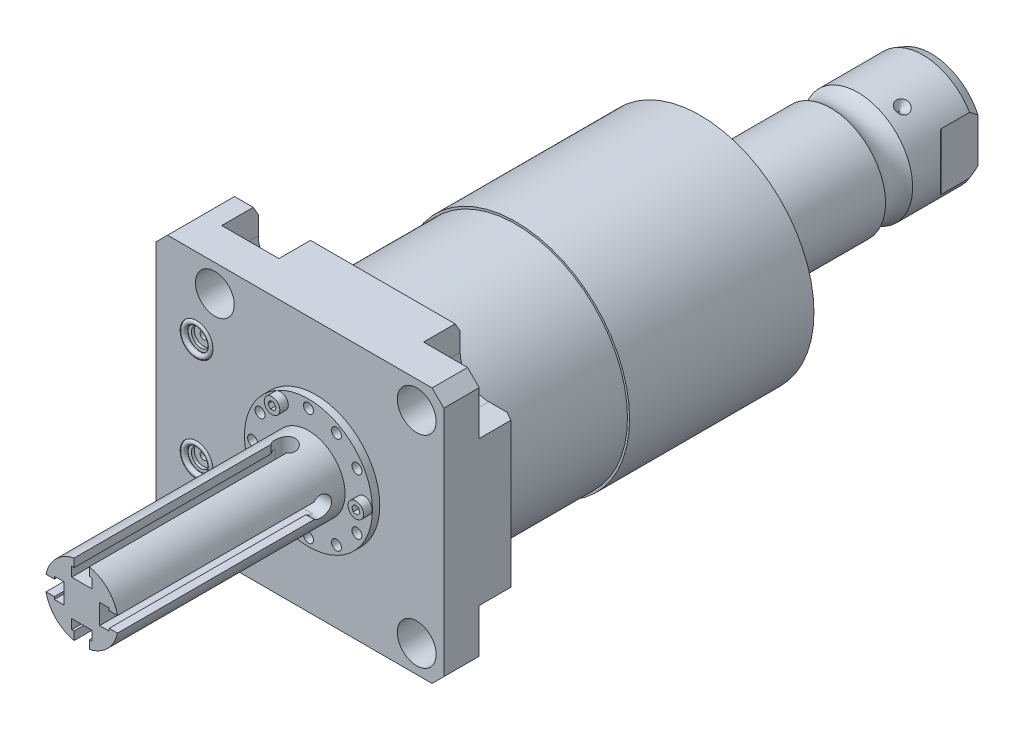
SolidWorks part; units mm, degrees
material "Alloy Steel"
ref_plane "Front Plane" through (0, 0, 0) normal (0, 0, 1) x (1, 0, 0)
ref_plane "Top Plane" through (0, 0, 0) normal (0, 1, 0) x (1, 0, 0)
ref_plane "Right Plane" through (0, 0, 0) normal (1, 0, 0) x (0, 0, -1)
sketch "Sketch1" plane through (0, 0, 0) normal (0, 0, 1) x (1, 0, 0)
  line L0 (-55.55, 44.45) -> (44.45, 44.45)
  line L1 (44.45, 44.45) -> (44.45, -44.45)
  line L2 (44.45, -44.45) -> (-55.55, -44.45)
  line L3 (-55.55, -44.45) -> (-55.55, 44.45)
  dimension "D1" = 100
  dimension "D2" = 88.9
  dimension "D3" = 44.45
  dimension "D4" = 44.45
extrude "Extrude1" add sketch "Sketch1" along normal blind 25.019
hole_wizard "Hole1" positions "Sketch22" profile "Sketch21" legacy end condition through all
sketch "Sketch22" plane through (0, 0, 0) normal (0, 0, -1) x (-1, 0, 0)
  line L0 (0, 0) -> (42.7441, 0) construction
  line L1 (0, 0.8532) -> (0, 27.5062) construction
  point P0 (-35.052, -35.052)
  point P9 (-35.052, 35.052)
  point P11 (35.052, 35.052)
  point P12 (35.052, -35.052)
  dimension "D1" = 35.052
  dimension "D2" = 35.052
sketch "Sketch21" plane through (35.052, -35.052, 0) normal (1, 0, 0) x (0, 1, 0)
  line L0 (0, 0) -> (0, 25.019)
  line L1 (0, 25.019) -> (6.7435, 25.019)
  line L2 (6.7435, 25.019) -> (6.7435, 0)
  line L3 (6.7435, 0) -> (0, 0)
  line L4 (0, 110) -> (0, -10) construction
  dimension "Diameter" = 13.487
  dimension "Depth" = 25.019
sketch "Sketch3" plane through (0, 0, 0) normal (0, 0, -1) x (-1, 0, 0)
  line L0 (-35.052, -25.1205) -> (-44.45, -25.1205)
  line L1 (-44.45, -44.45) -> (-44.45, -25.1205)
  line L2 (-44.45, 25.1205) -> (-44.45, 44.45)
  line L3 (-44.45, 25.1205) -> (-35.052, 25.1205)
  line L4 (-25.1205, 35.052) -> (-25.1205, 44.45)
  line L5 (-44.45, 44.45) -> (-25.1205, 44.45)
  line L6 (25.1205, 44.45) -> (25.1205, 35.052)
  line L7 (44.9835, 35.052) -> (44.9835, 44.45)
  line L8 (25.1205, 44.45) -> (44.9835, 44.45)
  line L9 (44.9835, -44.45) -> (25.1205, -44.45)
  line L10 (44.9835, -44.45) -> (44.9835, -35.052)
  line L11 (25.1205, -35.052) -> (25.1205, -44.45)
  line L12 (-25.1205, -44.45) -> (-44.45, -44.45)
  line L13 (-25.1205, -44.45) -> (-25.1205, -35.052)
  line L14 (-44.45, 44.45) -> (55.55, 44.45) construction
  line L15 (-44.45, -44.45) -> (-44.45, 44.45) construction
  line L16 (55.55, -44.45) -> (-44.45, -44.45) construction
  arc A0 (-25.1205, -35.052) -> (-35.052, -25.1205) centre (-35.052, -35.052) ccw
  arc A1 (-35.052, 25.1205) -> (-25.1205, 35.052) centre (-35.052, 35.052) ccw
  arc A2 (25.1205, 35.052) -> (44.9835, 35.052) centre (35.052, 35.052) ccw
  arc A3 (44.9835, -35.052) -> (25.1205, -35.052) centre (35.052, -35.052) ccw
  circle A8 centre (-35.052, 35.052) radius 6.7435 construction
  circle A9 centre (-35.052, -35.052) radius 6.7435 construction
  circle A10 centre (35.052, -35.052) radius 6.7435 construction
  circle A11 centre (35.052, 35.052) radius 6.7435 construction
  dimension "D1" = 9.9315
extrude "Cut-Extrude2" cut sketch "Sketch3" against normal blind 12.7
ref_plane "Plane16" through (0, 0, 12.014) normal (0, 0, 1) x (1, 0, 0)
sketch "Sketch23" plane through (0, 0, 12.014) normal (0, 0, 1) x (1, 0, 0)
  line L0 (-11.9397, -13.0048) -> (-61.0013, -13.0048) construction
  line L1 (-55.55, -23.749) -> (-55.296, -23.749)
  line L3 (-55.296, -23.749) -> (-55.296, -19.6596)
  line L4 (-55.296, -19.6596) -> (-54.5848, -18.9484)
  line L5 (-54.5848, -18.9484) -> (-41.1228, -18.9484)
  line L6 (-41.1228, -18.9484) -> (-41.1228, -13.0048)
  line L7 (-41.1228, -13.0048) -> (-55.55, -13.0048)
  line L8 (-55.55, -13.0048) -> (-55.55, -23.749)
  line L10 (-55.55, 44.45) -> (-55.55, -44.45) construction
  dimension "D1" = 21.4884
  dimension "D2" = 0.254
  dimension "D3" = 45
  dimension "D4" = 13.3096
  dimension "D5" = 11.8872
  dimension "D6" = 14.1732
  dimension "D7" = 13.0048
revolve "Cut-Revolve5" cut sketch "Sketch23" angle 360 about L0
mirror "Mirror1" about plane through (0, 0, 0) normal (0, 1, 0) of "Cut-Revolve5"
sketch "Sketch6" plane through (0, 0, 25.019) normal (0, 0, 1) x (1, 0, 0)
  line L0 (0, 0) -> (-71.0417, 0) construction
  circle A0 centre (-41.402, -18.11) radius 5.7023
  circle A1 centre (-41.402, 18.11) radius 5.7023
  dimension "D4" = 11.4046
  dimension "D1" = 18.11
  dimension "D2" = 36.22
  dimension "D3" = 41.402
extrude "Cut-Extrude3" cut sketch "Sketch6" against normal blind 1.4478
sketch "Sketch7" plane through (0, 0, 23.5712) normal (0, 0, 1) x (1, 0, 0)
  circle A0 centre (-41.402, 18.11) radius 3.2512
  circle A1 centre (-41.402, -18.11) radius 3.2512
  circle A2 centre (-41.402, 18.11) radius 5.7023 construction
  circle A3 centre (-41.402, -18.11) radius 5.7023 construction
  dimension "D1" = 6.5024
extrude "Cut-Extrude4" cut sketch "Sketch7" against normal blind 1.016
sketch "Sketch8" plane through (0, 0, 22.5552) normal (0, 0, 1) x (1, 0, 0)
  circle A0 centre (-41.402, 18.11) radius 1.2446
  circle A1 centre (-41.402, -18.11) radius 1.2446
  circle A2 centre (-41.402, 18.11) radius 5.7023 construction
  circle A3 centre (-41.402, -18.11) radius 5.7023 construction
  dimension "D1" = 2.4892
extrude "Cut-Extrude5" cut sketch "Sketch8" against normal blind 11.9888
ref_plane "Plane17" through (0, 18.11, 0) normal (0, 1, 0) x (-1, 0, 0)
sketch "Sketch9" plane through (-41.656, 18.11, 23.5712) normal (0, 1, 0) x (1, 0, 0)
  line L0 (0.254, -1.9469) -> (0.254, 0.0927) construction
  line L3 (-5.4483, 0) -> (5.9563, 0) construction
  line L4 (0.254, 13.0048) -> (0.254, 1.016) construction
  circle A0 centre (5.0292, -0.9271) radius 0.9271
  dimension "D1" = 1.8542
  dimension "D2" = 9.5504
revolve "Revolve1" add sketch "Sketch9" angle 360 about L0
mirror "Mirror2" about plane through (0, 0, 0) normal (0, 1, 0) of bodies 116
chamfer "Chamfer1" distance 4.064 angle 45 4 edges at (44.45, -44.45, 18.8595) (44.45, 44.45, 18.8595) (-55.55, 44.45, 12.5095) (-55.55, -44.45, 12.5095)
chamfer "Chamfer2" distance 3.0226 angle 30 5 edges at (-48.2347, -44.45, 0) (0, -44.45, 0) (44.45, 0, 0) (-48.2347, 44.45, 0) (0, 44.45, 0)
sketch "Sketch24" plane through (0, 0, 0) normal (1, 0, 0) x (0, 0, -1)
  line L0 (0, 0) -> (113.9127, 0) construction
  line L1 (0, 0) -> (0, 38.786)
  line L2 (0, 38.786) -> (44.45, 38.786)
  line L3 (44.45, 38.786) -> (44.45, 39.5225)
  line L4 (44.45, 39.5225) -> (108.4839, 39.5225)
  line L5 (108.4839, 39.5225) -> (112.268, 25.4)
  line L6 (112.268, 25.4) -> (112.268, 0)
  line L7 (112.268, 0) -> (0, 0)
  dimension "D1" = 77.572
  dimension "D2" = 44.45
  dimension "D3" = 79.045
  dimension "D4" = 50.8
  dimension "D5" = 15
  dimension "D6" = 112.268
revolve "Revolve4" add sketch "Sketch24" angle 360 about L0
sketch "Sketch17" plane through (0, 0, 0) normal (1, 0, 0) x (0, 0, -1)
  line L0 (112.268, 0) -> (112.268, -19.05)
  line L1 (112.268, -19.05) -> (153.8149, -19.05)
  line L2 (163.2291, -19.05) -> (185.776, -19.05)
  line L3 (188.697, -17.9868) -> (188.697, 0)
  line L4 (188.697, 0) -> (112.268, 0)
  line L5 (130.8989, 0) -> (0.816, 0) construction
  line L6 (112.268, -25.4) -> (112.268, 25.4) construction
  line L7 (-25.019, -40.386) -> (-25.019, 40.386) construction
  line L8 (188.697, -17.9868) -> (185.776, -19.05)
  arc A0 (163.2291, -19.05) -> (153.8149, -19.05) centre (158.522, -25.4254) ccw
  dimension "D2" = 20
  dimension "D4" = 7.9248
  dimension "D5" = 35.0012
  dimension "D1" = 213.716
  dimension "D3" = 38.1
  dimension "D6" = 30.175
  dimension "D7" = 2.921
revolve "Revolve3" add sketch "Sketch17" angle 360 about L5
sketch "Sketch28" plane through (0, 0, 0) normal (0, 1, 0) x (1, 0, 0)
  line L0 (-34.3062, 169.19) -> (35.4095, 169.19) construction
  line L1 (-19.05, 171.603) -> (-16.637, 169.19)
  line L2 (-19.05, 185.776) -> (-19.05, 163.2291) construction
  line L3 (-16.637, 169.19) -> (-19.05, 169.19)
  line L4 (-19.05, 169.19) -> (-19.05, 171.603)
  arc A0 (-19.05, 153.8149) -> (-19.05, 163.2291) centre (-25.4254, 158.522) ccw construction
  dimension "D3" = 10.668
  dimension "D1" = 45
  dimension "D2" = 4.826
revolve "Cut-Revolve6" cut sketch "Sketch28" angle 360 about L0
pattern_circular "CirPattern1" count 3 over 360 about axis through (0, 0, -130.8989) along (0, 0, -1) of "Cut-Revolve6"
hole_wizard "Hole2" positions "Sketch33" profile "Sketch32" legacy
sketch "Sketch33" plane through (0, 0, -188.697) normal (0, 0, -1) x (-1, 0, 0)
  circle A0 centre (0, 0) radius 19.05 construction
  point P0 (0, 0)
sketch "Sketch32" plane through (0, 0, -188.697) normal (1, 0, 0) x (0, 1, 0)
  line L0 (0, 0) -> (0, 29.5665)
  line L1 (0, 29.5665) -> (6.9342, 25.4)
  line L2 (6.9342, 25.4) -> (6.9342, 0)
  line L4 (6.9342, 0) -> (0, 0)
  line L6 (0, 29.5665) -> (-6.9342, 25.4) construction
  line L7 (0, -4.2442) -> (0, 117.3081) construction
  dimension "Diameter" = 13.8684
  dimension "Depth" = 25.4
  dimension "Drill Angle" = 118
sketch "Sketch34" plane through (0, 0, 0) normal (0, 1, 0) x (0, 0, -1)
  line L0 (0, 0) -> (211.3651, 0) construction
  line L1 (172.9129, 19.05) -> (175.4582, 16.5047)
  line L3 (175.997, 16.2815) -> (188.697, 16.2815)
  line L4 (188.697, -17.9868) -> (188.697, 17.9868) construction
  line L5 (188.697, 16.2815) -> (188.697, 19.05)
  line L6 (188.697, 19.05) -> (172.9129, 19.05)
  line L7 (188.697, -19.05) -> (172.9129, -19.05)
  line L8 (188.697, -16.2815) -> (188.697, -19.05)
  line L9 (175.997, -16.2815) -> (188.697, -16.2815)
  line L10 (172.9129, -19.05) -> (175.4582, -16.5047)
  line L11 (185.776, 19.05) -> (171.603, 19.05) construction
  arc A0 (175.997, 16.2815) -> (175.4582, 16.5047) centre (175.997, 17.0435) cw
  arc A1 (175.997, -16.2815) -> (175.4582, -16.5047) centre (175.997, -17.0435) ccw
  dimension "D2" = 0.762
  dimension "D1" = 45
  dimension "D3" = 12.7
  dimension "D4" = 32.563
extrude "Cut-Extrude8" cut sketch "Sketch34" against normal through all and the other way through all
sketch "Sketch35" plane through (0, 0, 0) normal (0, 1, 0) x (1, 0, 0)
  line L0 (0, -985.6905) -> (0, 49014.3095) construction
  line L3 (0, -25.019) -> (22.225, -25.019)
  line L4 (40.386, -25.019) -> (-51.486, -25.019) construction
  line L5 (22.225, -25.019) -> (22.225, -27.559)
  line L6 (22.225, -27.559) -> (12.7, -27.559)
  line L7 (12.7, -27.559) -> (12.7, -106.299)
  line L8 (12.7, -106.299) -> (0, -106.299)
  line L9 (0, -106.299) -> (0, -25.019)
  dimension "D1" = 25.4
  dimension "D2" = 44.4501
  dimension "D3" = 2.54
  dimension "D4" = 81.28
revolve "Revolve5" add sketch "Sketch35" angle 360 about L0
sketch "Sketch36" plane through (0, 0, 27.559) normal (0, 0, 1) x (1, 0, 0)
  line L0 (0, -1000) -> (0, 49000) construction
  line L1 (-1000, 0) -> (49000, 0) construction
  line L2 (0, 0) -> (43301.2702, 25000) construction
  line L3 (0, 0) -> (25000, 43301.2702) construction
  circle A0 centre (0, 0) radius 19.431 construction
  circle A1 centre (19.4005, 0) radius 1.7272
  circle A2 centre (16.8278, 9.7155) radius 1.7272
  circle A3 centre (9.7155, 16.8278) radius 1.7272
  circle A4 centre (0, 19.431) radius 1.7272
  circle A5 centre (-9.7155, 16.8278) radius 1.7272
  circle A6 centre (-16.8278, 9.7155) radius 1.7272
  circle A7 centre (-19.4005, 0) radius 1.7272
  circle A8 centre (-16.8278, -9.7155) radius 1.7272
  circle A9 centre (-9.7155, -16.8278) radius 1.7272
  circle A10 centre (0, -19.431) radius 1.7272
  circle A11 centre (9.7155, -16.8278) radius 1.7272
  circle A12 centre (16.8278, -9.7155) radius 1.7272
  dimension "D3" = 38.8621
  dimension "D4" = 3.4544
  dimension "D5" = 3.4544
  dimension "D6" = 3.4544
  dimension "D7" = 3.4544
  dimension "D1" = 30
  dimension "D2" = 30
extrude "Cut-Extrude9" cut sketch "Sketch36" against normal up to surface (2.54 mm away) up to face at (22.225, 0, 25.019)
sketch "Sketch37" plane through (0, 0, 27.559) normal (0, 0, 1) x (1, 0, 0)
  circle A0 centre (19.4005, 0) radius 2.7051
  circle A1 centre (-9.7155, 16.8278) radius 2.7051
  circle A2 centre (-9.7155, -16.8278) radius 2.7051
  dimension "D1" = 5.4102
  dimension "D2" = 5.4102
  dimension "D3" = 5.4102
extrude "Extrude2" add sketch "Sketch37" along normal blind 2.9464
sketch "Sketch38" plane through (0, 0, 30.5054) normal (0, 0, 1) x (1, 0, 0)
  line L1 (19.8647, -1.3667) -> (20.8162, -0.2814)
  line L2 (20.8162, -0.2814) -> (20.352, 1.0853)
  line L3 (20.352, 1.0853) -> (18.9363, 1.3667)
  line L4 (18.9363, 1.3667) -> (17.9848, 0.2814)
  line L5 (17.9848, 0.2814) -> (18.449, -1.0853)
  line L6 (18.449, -1.0853) -> (19.8647, -1.3667)
  line L7 (-8.849, 15.6734) -> (-8.2826, 17.001)
  line L8 (-8.2826, 17.001) -> (-9.1491, 18.1554)
  line L9 (-9.1491, 18.1554) -> (-10.582, 17.9821)
  line L10 (-10.582, 17.9821) -> (-11.1485, 16.6545)
  line L11 (-11.1485, 16.6545) -> (-10.2819, 15.5002)
  line L12 (-10.2819, 15.5002) -> (-8.849, 15.6734)
  line L13 (-9.365, -18.2279) -> (-8.3277, -17.2243)
  line L14 (-8.3277, -17.2243) -> (-8.6782, -15.8242)
  line L15 (-8.6782, -15.8242) -> (-10.066, -15.4276)
  line L16 (-10.066, -15.4276) -> (-11.1034, -16.4312)
  line L17 (-11.1034, -16.4312) -> (-10.7529, -17.8314)
  line L18 (-10.7529, -17.8314) -> (-9.365, -18.2279)
  circle A0 centre (19.4005, 0) radius 1.25 construction
  circle A1 centre (-9.7155, 16.8278) radius 1.25 construction
  circle A2 centre (-9.7155, -16.8278) radius 1.25 construction
  dimension "D1" = 2.5
  dimension "D2" = 2.5
  dimension "D3" = 2.5
extrude "Cut-Extrude10" cut sketch "Sketch38" against normal blind 2.032
ref_plane "Plane18-slot-angle" through (0, 0, 0) normal (1, 0, 0) x (0, 0, -1)
ref_plane "Plane19" through (0, 0, 0) normal (0, 1, 0) x (-1, 0, 0)
ref_plane "Plane20" through (0, 12.7, 66.929) normal (0, 1, 0) x (-1, 0, 0)
sketch "Sketch39" plane through (0, 12.7, 66.929) normal (0, 1, 0) x (-1, 0, 0)
  line L0 (0, -1016.9858) -> (0, 48983.0142) construction
  line L2 (-2.6416, 39.37) -> (-2.6416, -28.9574)
  line L3 (12.7, 39.37) -> (-12.7, 39.37) construction
  line L4 (-2.6416, 39.37) -> (2.6416, 39.37)
  line L5 (2.6416, 39.37) -> (2.6416, -28.9574)
  arc A0 (-2.6416, -28.9574) -> (2.6416, -28.9574) centre (0, -31.242) ccw
  point P11 (0, 39.37)
  dimension "D1" = 6.985
  dimension "D2" = 5.2832
  dimension "D3" = 70.612
extrude "Cut-Extrude11" cut sketch "Sketch39" against normal blind 6.477
sketch "Sketch40" plane through (0, 6.223, 0) normal (0, 1, 0) x (1, 0, 0)
  line L0 (0, -1067.8204) -> (0, 48932.1796) construction
  line L2 (-1000, -35.687) -> (49000, -35.687) construction
  line L3 (-3.4925, -35.687) -> (3.4925, -35.687)
  line L4 (3.4925, -35.687) -> (3.4925, -106.299)
  line L5 (-12.7, -106.299) -> (12.7, -106.299) construction
  line L6 (3.4925, -106.299) -> (-3.4925, -106.299)
  line L7 (-3.4925, -35.687) -> (-3.4925, -106.299)
  point P12 (0, -35.687)
  point P13 (0, -106.299)
  dimension "D1" = 6.985
extrude "Cut-Extrude12" cut sketch "Sketch40" along normal blind 3.302
mirror "Mirror3" about plane through (0, 0, 0) normal (0, 1, 0) of "Cut-Extrude12", "Cut-Extrude11"
pattern_circular "CirPattern2" count 2 every 90 about axis through (0, 0, 0) along (0, 0, 1) of "Mirror3", "Cut-Extrude11", "Cut-Extrude12"
